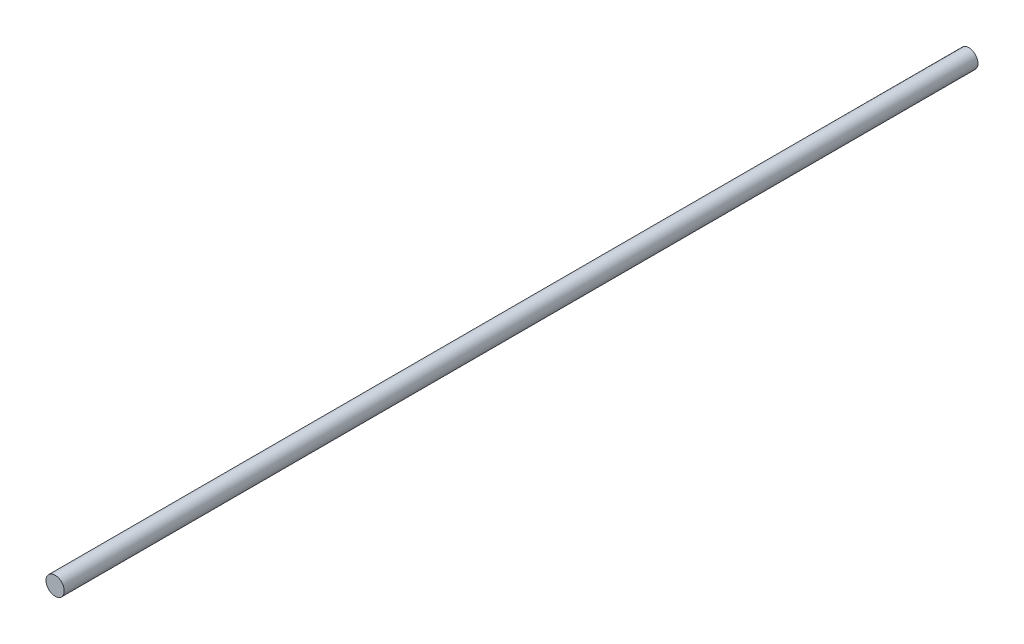
SolidWorks part; units mm, degrees
ref_plane "Front Plane" through (0, 0, 0) normal (0, 0, 1) x (1, 0, 0)
ref_plane "Top Plane" through (0, 0, 0) normal (0, 1, 0) x (1, 0, 0)
ref_plane "Right Plane" through (0, 0, 0) normal (1, 0, 0) x (0, 0, -1)
sketch "Sketch1" plane through (0, 0, 0) normal (0, 0, 1) x (1, 0, 0)
  circle A0 centre (0, 0) radius 4
  dimension "D1" = 8
extrude "Boss-Extrude1" add sketch "Sketch1" along normal mid plane 400
